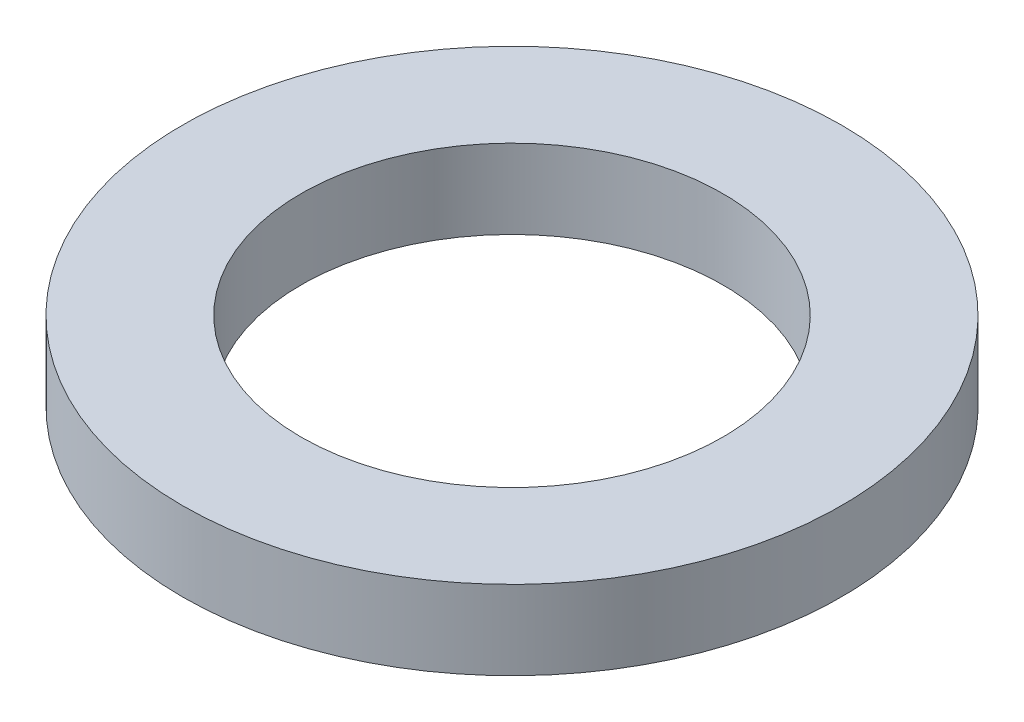
SolidWorks part; units mm, degrees
ref_plane "Front Plane" through (0, 0, 0) normal (0, 0, 1) x (1, 0, 0)
ref_plane "Top Plane" through (0, 0, 0) normal (0, 1, 0) x (1, 0, 0)
ref_plane "Right Plane" through (0, 0, 0) normal (1, 0, 0) x (0, 0, -1)
sketch "Sketch1" plane through (0, 0, 0) normal (0, 1, 0) x (1, 0, 0)
  circle A0 centre (0, 0) radius 1.6
  circle A1 centre (0, 0) radius 2.5
  dimension "D1" = 3.2
  dimension "D2" = 5
extrude "Boss-Extrude1" add sketch "Sketch1" along normal blind 0.6
ref_plane "Plane1" through (0, 0.3, 0) normal (0, 1, 0) x (1, 0, 0)
ref_plane "Plane2" through (0, 0.3, 0) normal (0, -1, 0) x (-1, 0, 0)
